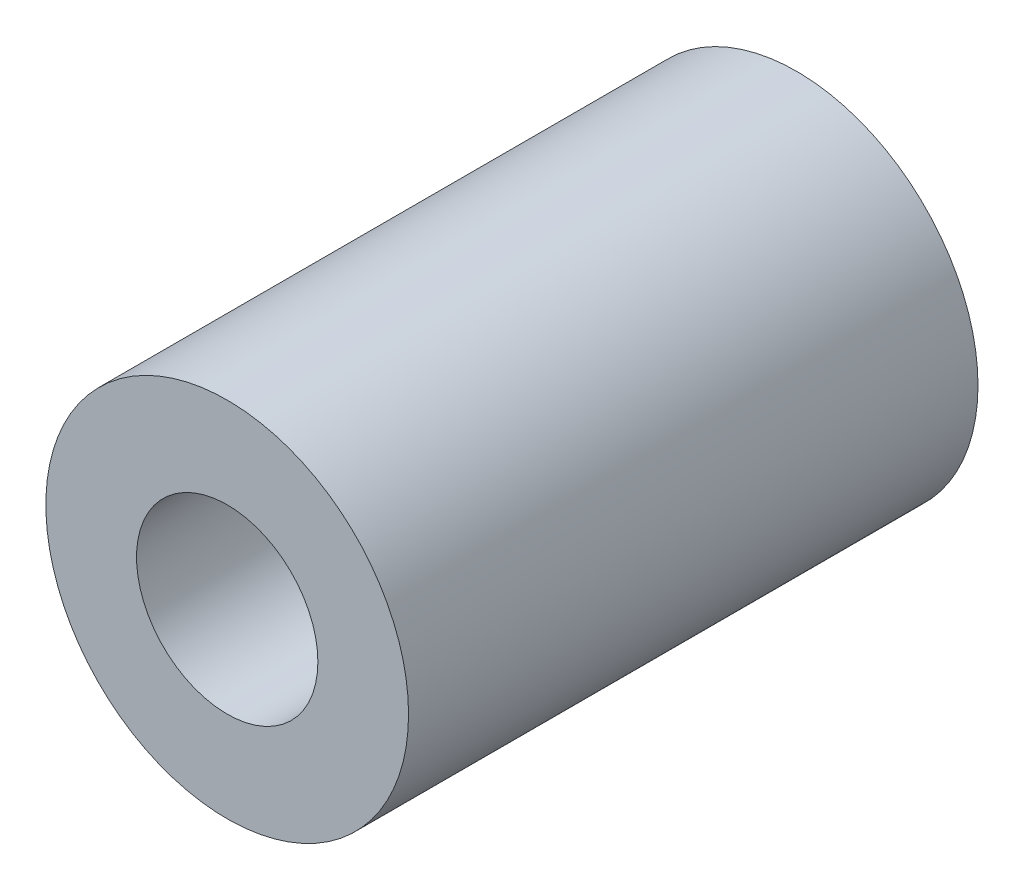
SolidWorks part; units mm, degrees
ref_plane "Front Plane" through (0, 0, 0) normal (0, 0, 1) x (1, 0, 0)
ref_plane "Top Plane" through (0, 0, 0) normal (0, 1, 0) x (1, 0, 0)
ref_plane "Right Plane" through (0, 0, 0) normal (1, 0, 0) x (0, 0, -1)
sketch "Sketch1" plane through (0, 0, 0) normal (0, 0, 1) x (1, 0, 0)
  circle A0 centre (0, 0) radius 5
  dimension "D1" = 10
extrude "Boss-Extrude1" add sketch "Sketch1" along normal blind 15.7
hole_wizard "Ø5.0mm Dowel Hole1" positions "Sketch2" profile "Sketch3" hole size "Ø5.0" standard "ANSI Metric" end condition up to next
sketch "Sketch2" plane through (0, 0, 15.7) normal (0, 0, 1) x (1, 0, 0)
  point P0 (0, 0)
sketch "Sketch3" plane through (0, 0, 15.7) normal (1, 0, 0) x (0, -1, 0)
  line L0 (0, 0) -> (0, 15.7)
  line L1 (0, 15.7) -> (2.5, 15.7)
  line L2 (2.5, 15.7) -> (2.5, 0)
  line L5 (2.5, 0) -> (0, 0)
  line L11 (0, -6.35) -> (0, 107.95) construction
  dimension "Thru Hole Dia." = 5
  dimension "Thru Hole Depth" = 15.7
